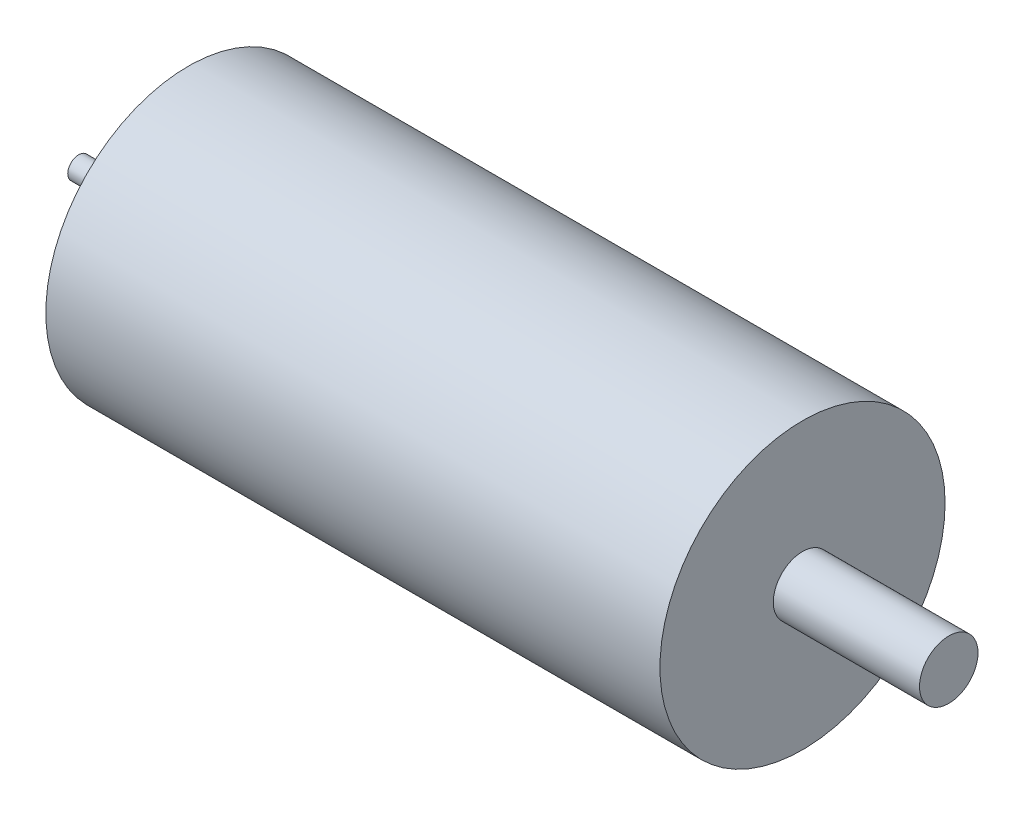
SolidWorks part; units mm, degrees
ref_plane "Front Plane" through (0, 0, 0) normal (0, 0, 1) x (1, 0, 0)
ref_plane "Top Plane" through (0, 0, 0) normal (0, 1, 0) x (1, 0, 0)
ref_plane "Right Plane" through (0, 0, 0) normal (1, 0, 0) x (0, 0, -1)
sketch "Sketch1" plane through (0, 0, 0) normal (1, 0, 0) x (0, 0, -1)
  circle A0 centre (0, 0) radius 19.5
  dimension "D1" = 39
extrude "Boss-Extrude1" add sketch "Sketch1" along normal blind 84
sketch "Sketch2" plane through (84, 0, 0) normal (1, 0, 0) x (0, 0, -1)
  circle A0 centre (0, 0) radius 4
  dimension "D1" = 8
extrude "Boss-Extrude2" add sketch "Sketch2" along normal blind 20
sketch "Sketch3" plane through (0, 0, 0) normal (-1, 0, 0) x (0, 0, 1)
  circle A0 centre (0, 0) radius 1.5
  dimension "D1" = 3
extrude "Boss-Extrude3" add sketch "Sketch3" along normal blind 15
